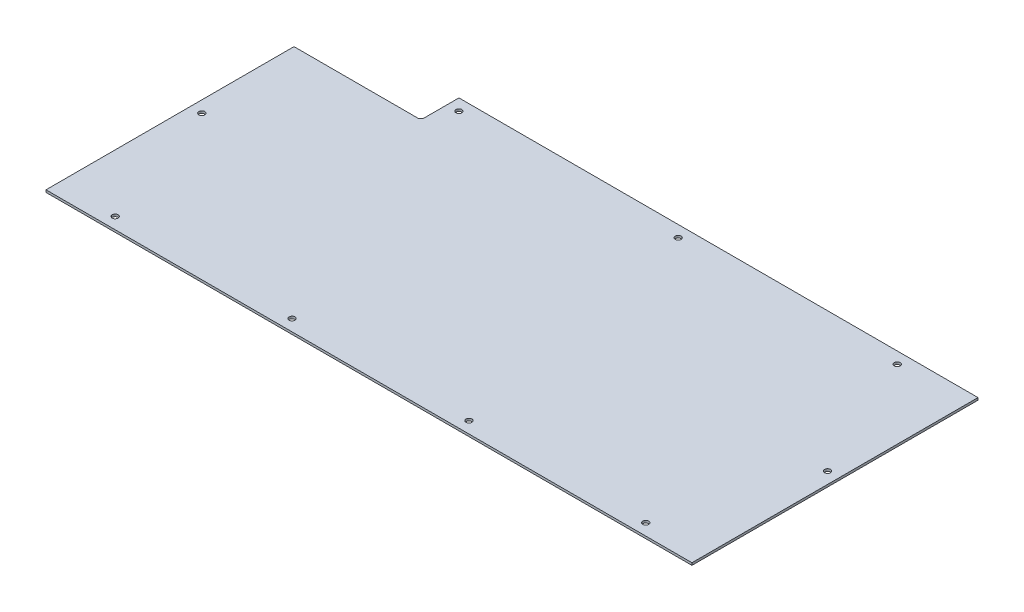
SolidWorks part; units mm, degrees
ref_plane "Front Plane" through (0, 0, 0) normal (0, 0, 1) x (1, 0, 0)
ref_plane "Top Plane" through (0, 0, 0) normal (0, 1, 0) x (1, 0, 0)
ref_plane "Right Plane" through (0, 0, 0) normal (1, 0, 0) x (0, 0, -1)
sketch "Sketch1" plane through (0, 0, 0) normal (0, 1, 0) x (1, 0, 0)
  line L0 (-288.1444, 87.3934) -> (-181.1444, 87.3932)
  line L1 (-288.1444, -127.6068) -> (271.8556, -127.6068)
  line L2 (-288.1444, -127.6068) -> (-288.1444, 87.3934)
  line L3 (-178.1444, 120.3932) -> (271.8556, 120.3932)
  line L4 (271.8556, -127.6068) -> (271.8556, 120.3932)
  line L5 (-288.1444, -127.6068) -> (271.8556, 120.3932) construction
  line L7 (-178.1444, 90.3932) -> (-178.1444, 120.3932)
  arc A0 (-178.1444, 90.3932) -> (-181.1444, 87.3932) centre (-181.1444, 90.3932) cw
  circle A1 centre (211.8556, 110.3932) radius 2.55
  circle A2 centre (-168.1444, 110.3932) radius 2.55
  circle A3 centre (21.8556, 110.3932) radius 2.55
  circle A4 centre (-238.1444, -117.6068) radius 2.55
  circle A5 centre (-84.811, -117.6068) radius 2.55
  circle A6 centre (68.5223, -117.6068) radius 2.55
  circle A7 centre (221.8556, -117.6068) radius 2.55
  circle A8 centre (261.8556, 0) radius 2.55
  circle A9 centre (-278.1444, -2.55) radius 2.55
  point P0 (0, 0)
  dimension "D3" = 3
  dimension "D6" = 10
  dimension "D7" = 10
  dimension "D8" = 120
  dimension "D9" = 60
  dimension "D10" = 190
  dimension "D11" = 10
  dimension "D12" = 5.1
  dimension "D13" = 4
  dimension "D14" = 50
  dimension "D15" = 50
  dimension "D16" = 10
  dimension "D17" = 10
  dimension "D18" = 190
  dimension "D1" = 560
  dimension "D2" = 248
  dimension "D4" = 110
  dimension "D5" = 30
extrude "Boss-Extrude1" add sketch "Sketch1" along normal blind 2
